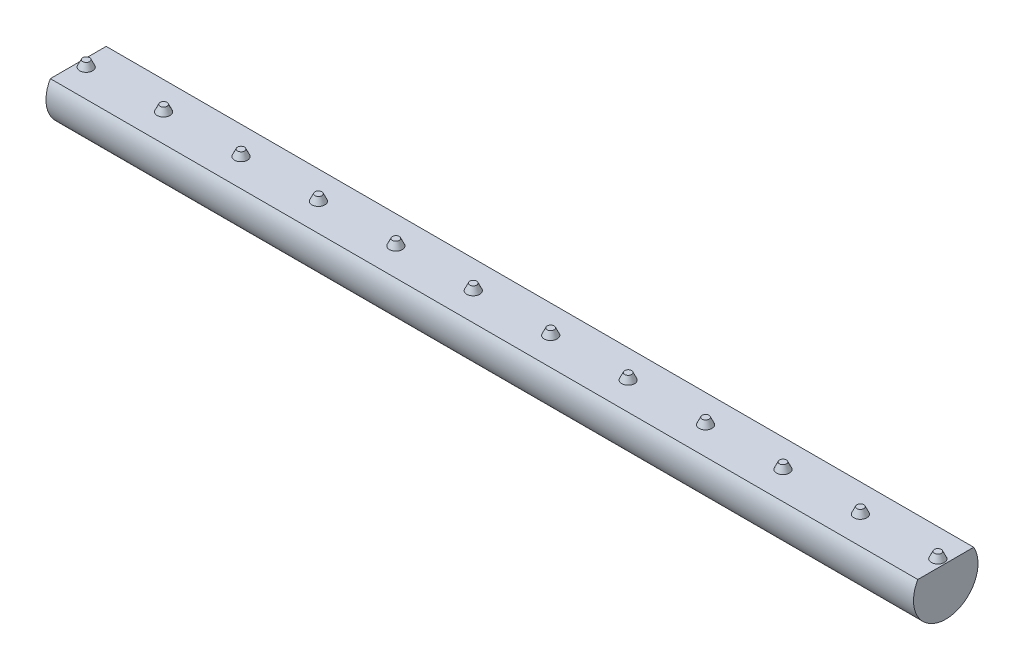
SolidWorks part; units mm, degrees
ref_plane "Ebene vorne" through (0, 0, 0) normal (0, 0, 1) x (1, 0, 0)
ref_plane "Ebene oben" through (0, 0, 0) normal (0, 1, 0) x (1, 0, 0)
ref_plane "Ebene rechts" through (0, 0, 0) normal (1, 0, 0) x (0, 0, -1)
sketch "Skizze1" plane through (0, 0, 0) normal (1, 0, 0) x (0, 0, -1)
  line L0 (-4.3301, 2.5) -> (4.3301, 2.5)
  arc A0 (-4.3301, 2.5) -> (4.3301, 2.5) centre (0, 0) ccw
  dimension "D1" = 10
  dimension "D2" = 2.5
extrude "Aufsatz-Linear austragen1" add sketch "Skizze1" along normal blind 134.46
ref_plane "Ebene1" through (67.23, 0, 0) normal (1, 0, 0) x (0, 0, -1)
ref_plane "Ebene2" through (0, 0, -5) normal (0, 0, -1) x (-1, 0, 0)
ref_plane "Ebene3" through (0, 0, 5) normal (0, 0, 1) x (1, 0, 0)
ref_plane "Ebene4" through (0, 0, 0) normal (0, 0, 1) x (1, 0, 0)
sketch "Skizze3" plane through (0, 2.5, 0) normal (0, 1, 0) x (1, 0, 0)
  line L0 (0, 4.3301) -> (0, -4.3301) construction
  line L1 (-10.7815, 0) -> (10.7815, 0) construction
  circle A0 centre (1.229, 0) radius 1
  dimension "D1" = 1.229
  dimension "D2" = 2
extrude "Aufsatz-Linear austragen2" add sketch "Skizze3" along normal blind 1 draft 25
pattern_linear "Lineares Muster2" count 12 spacing 12 along (1, 0, 0) of "Aufsatz-Linear austragen2"
